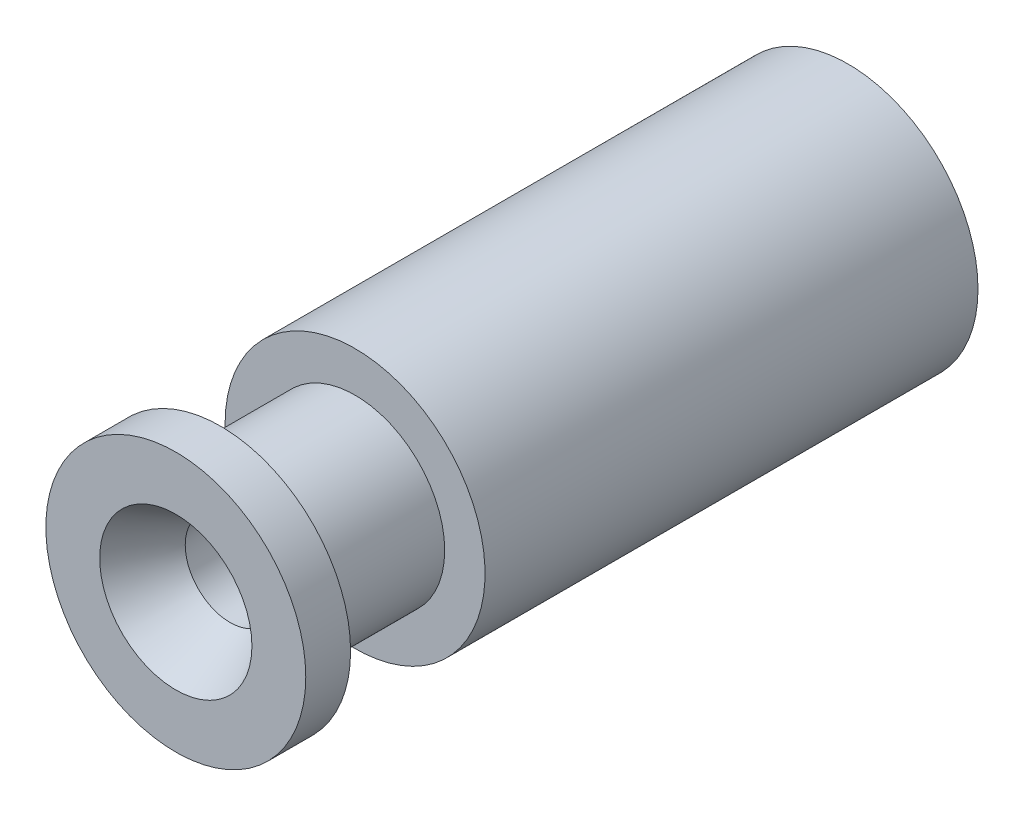
SolidWorks part; units mm, degrees
ref_plane "Front Plane" through (0, 0, 0) normal (0, 0, 1) x (1, 0, 0)
ref_plane "Top Plane" through (0, 0, 0) normal (0, 1, 0) x (1, 0, 0)
ref_plane "Right Plane" through (0, 0, 0) normal (1, 0, 0) x (0, 0, -1)
sketch "Sketch1" plane through (0, 0, 0) normal (0, 0, 1) x (1, 0, 0)
  circle A0 centre (0, 0) radius 2.9
  dimension "D1" = 5.8
extrude "Boss-Extrude1" add sketch "Sketch1" along normal blind 15
sketch "Sketch2" plane through (0, 0, 0) normal (0, 0, -1) x (-1, 0, 0)
  circle A0 centre (0, 0) radius 1
  dimension "D1" = 2
extrude "Cut-Extrude1" cut sketch "Sketch2" against normal through all
hole_wizard "Tap Drill for M3x0.5 Tap1" positions "Sketch4" profile "Sketch3" hole size "M3x0.5" standard "Ansi Metric"
sketch "Sketch4" plane through (0, 0, 0) normal (0, 0, -1) x (-1, 0, 0)
  point P0 (0, 0)
sketch "Sketch3" plane through (0, 0, 0) normal (1, 0, 0) x (0, 1, 0)
  line L0 (0, 0) -> (0, 11.7511)
  line L1 (0, 11.7511) -> (1.25, 11)
  line L2 (1.25, 11) -> (1.25, 0)
  line L5 (1.25, 0) -> (0, 0)
  line L10 (0, 11.7511) -> (-1.25, 11) construction
  line L11 (0, -6.35) -> (0, 107.95) construction
  dimension "Hole Dia." = 2.5
  dimension "Hole Depth" = 11
  dimension "Drill Angle" = 118
cosmetic thread "Cosmetic Thread1" parameters "D1"=10, "D2"=3
sketch "Sketch5" plane through (0, 0, 0) normal (1, 0, 0) x (0, 0, -1)
  line L0 (0, 0) -> (-16.1108, 0) construction
  line L1 (-14, 3.7938) -> (-11, 3.7938)
  line L2 (-14, 3.7938) -> (-14, 2)
  line L3 (-14, 2) -> (-11, 2)
  line L4 (-11, 3.7938) -> (-11, 2)
  dimension "D1" = 11
  dimension "D2" = 14
  dimension "D3" = 4
revolve "Cut-Revolve1" cut sketch "Sketch5" angle 360 about L0
chamfer "Chamfer1" distance 0.75 angle 60 1 edges at (-1.25, 0, 0)
chamfer "Chamfer2" distance 1.21 angle 30 1 edges at (-1, 0, 15)
